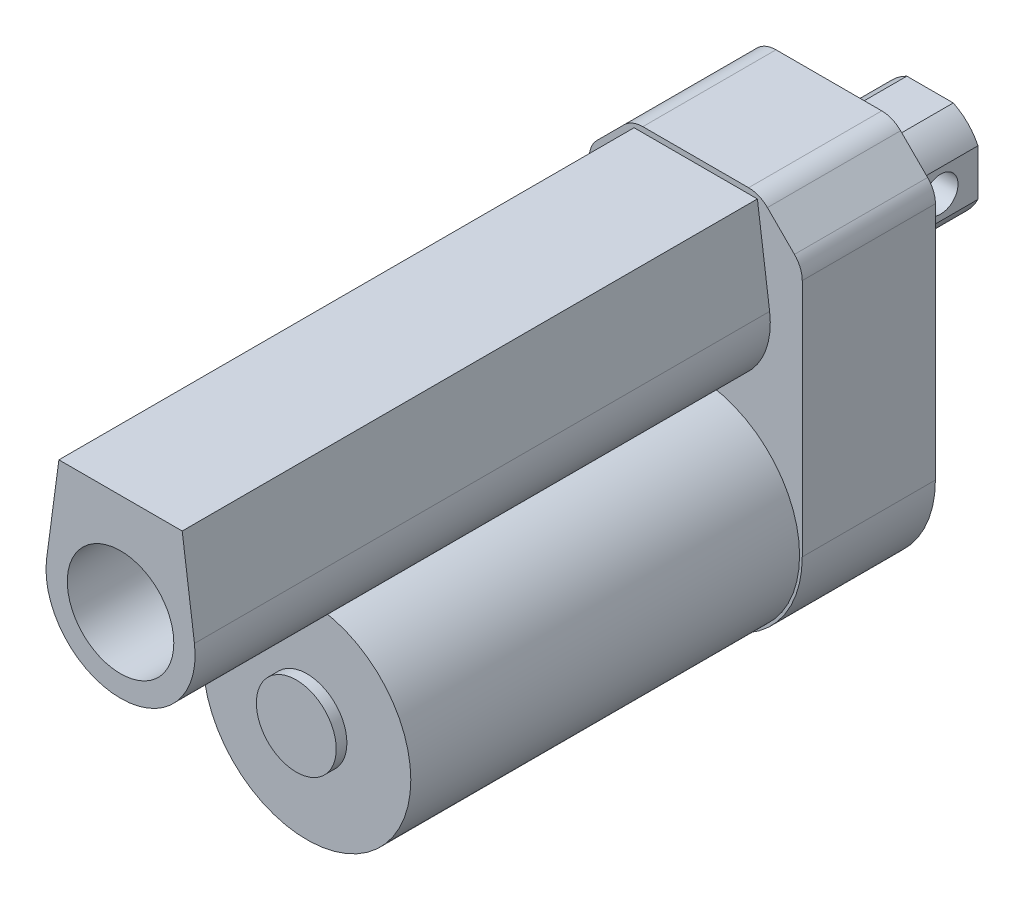
SolidWorks part; units mm, degrees
ref_plane "前视基准面" through (0, 0, 0) normal (0, 0, 1) x (1, 0, 0)
ref_plane "上视基准面" through (0, 0, 0) normal (0, 1, 0) x (1, 0, 0)
ref_plane "右视基准面" through (0, 0, 0) normal (1, 0, 0) x (0, 0, -1)
sketch "草图1" plane through (0, 0, 0) normal (0, 0, 1) x (1, 0, 0)
  line L0 (-20, 0) -> (-20, 44.9289)
  line L1 (-9.9289, 55) -> (9.9289, 55)
  line L2 (20, 44.9289) -> (20, 0)
  line L3 (-18.5355, 48.4645) -> (-13.4645, 53.5355)
  line L4 (13.4645, 53.5355) -> (18.5355, 48.4645)
  arc A0 (-20, 0) -> (20, 0) centre (0, 0) ccw
  arc A1 (-20, 44.9289) -> (-18.5355, 48.4645) centre (-15, 44.9289) cw
  arc A2 (20, 44.9289) -> (18.5355, 48.4645) centre (15, 44.9289) ccw
  arc A3 (13.4645, 53.5355) -> (9.9289, 55) centre (9.9289, 50) ccw
  arc A4 (-13.4645, 53.5355) -> (-9.9289, 55) centre (-9.9289, 50) cw
  point P4 (-20, 55)
  point P6 (20, 55)
  point P13 (-20, 47)
  point P16 (20, 47)
  point P19 (12, 55)
  point P22 (-12, 55)
  dimension "D1" = 40
  dimension "D2" = 55
  dimension "D3" = 5
  dimension "D4" = 5
extrude "凸台-拉伸1" add sketch "草图1" along normal blind 25
sketch "草图2" plane through (0, 0, 25) normal (0, 0, 1) x (1, 0, 0)
  circle A0 centre (0, 0) radius 19.5
  dimension "D1" = 39
extrude "凸台-拉伸2" add sketch "草图2" along normal blind 73
sketch "草图3" plane through (0, 0, 98) normal (0, 0, 1) x (1, 0, 0)
  circle A0 centre (0, 0) radius 7.5
  dimension "D1" = 15
extrude "凸台-拉伸3" add sketch "草图3" along normal blind 2
sketch "草图4" plane through (0, 0, 25) normal (0, 0, 1) x (1, 0, 0)
  line L0 (9.9289, 55) -> (-9.9289, 55) construction
  line L1 (-11.5765, 54) -> (-13.8757, 36.8615)
  line L3 (11.5765, 54) -> (13.8757, 36.8615)
  line L6 (0, 20.7202) -> (0, 56.7049) construction
  line L7 (-20, 44.9289) -> (-20, 0) construction
  line L8 (20, 0) -> (20, 44.9289) construction
  line L9 (-11.5765, 54) -> (11.5765, 54)
  arc A0 (-13.8757, 36.8615) -> (13.8757, 36.8615) centre (0, 35) ccw
  dimension "D1" = 28
  dimension "D2" = 20
  dimension "D3" = 1
extrude "凸台-拉伸4" add sketch "草图4" along normal blind 108
sketch "草图5" plane through (0, 0, 133) normal (0, 0, 1) x (1, 0, 0)
  circle A0 centre (0, 35) radius 10
  dimension "D1" = 20
extrude "切除-拉伸1" cut sketch "草图5" against normal blind 410
sketch "草图6" plane through (0, 0, 0) normal (0, 0, -1) x (-1, 0, 0)
  line L0 (-30.2846, 35) -> (34.2706, 35) construction
  line L1 (0, 69.8123) -> (0, -26.886) construction
  line L2 (-9.9289, 55) -> (9.9289, 55) construction
  line L4 (-4.3589, 44) -> (4.3589, 44)
  line L5 (-9, 39.3589) -> (-9, 30.6411)
  line L6 (-4.3589, 26) -> (4.3589, 26)
  line L7 (9, 39.3589) -> (9, 30.6411)
  arc A0 (-4.3589, 44) -> (-9, 39.3589) centre (0, 35) ccw
  arc A1 (9, 39.3589) -> (4.3589, 44) centre (0, 35) ccw
  arc A2 (-9, 30.6411) -> (-4.3589, 26) centre (0, 35) ccw
  arc A3 (4.3589, 26) -> (9, 30.6411) centre (0, 35) ccw
  dimension "D3" = 20
  dimension "D1" = 20
  dimension "D2" = 18
  dimension "D4" = 18
extrude "凸台-拉伸5" add sketch "草图6" along normal blind 19
sketch "草图7" plane through (9, 0, 0) normal (1, 0, 0) x (0, 0, -1)
  line L0 (26.7064, 35) -> (-8.4403, 35) construction
  line L2 (19, 44) -> (0, 44) construction
  line L3 (19, 26) -> (0, 26) construction
  line L4 (19, 39.3589) -> (19, 30.6411) construction
  circle A0 centre (12, 35) radius 3.25
  dimension "D1" = 6.5
  dimension "D2" = 7
extrude "切除-拉伸2" cut sketch "草图7" against normal blind 94
